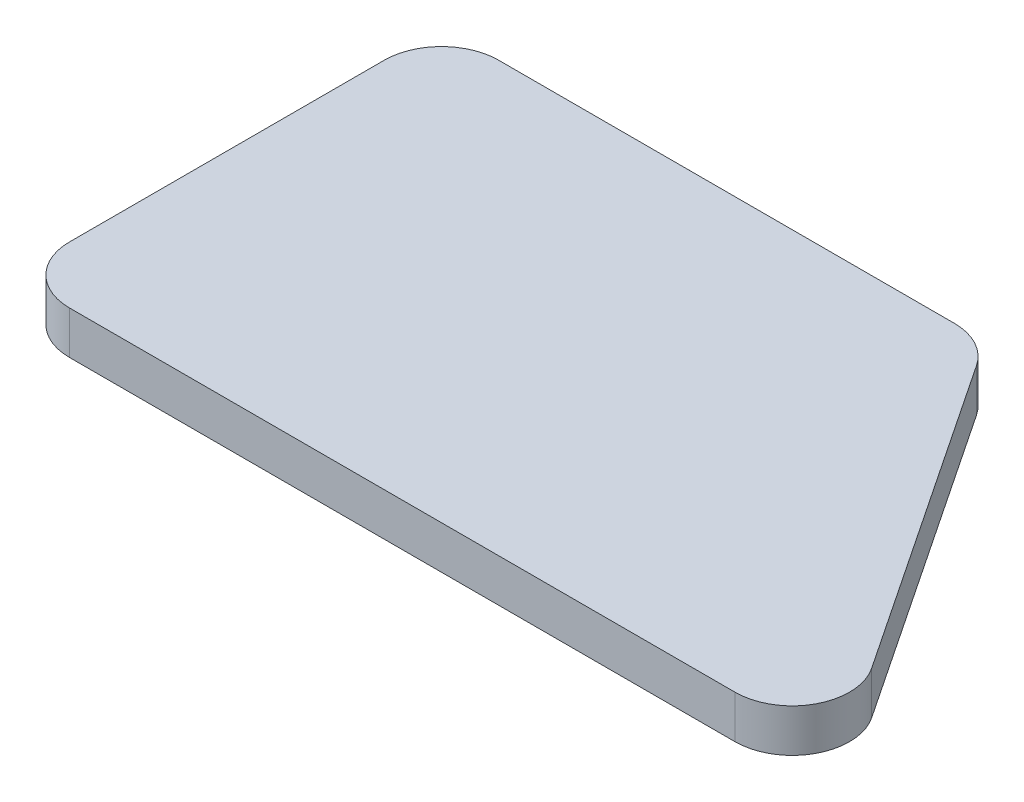
SolidWorks part; units mm, degrees
ref_plane "前视基准面" through (0, 0, 0) normal (0, 0, 1) x (1, 0, 0)
ref_plane "上视基准面" through (0, 0, 0) normal (0, 1, 0) x (1, 0, 0)
ref_plane "右视基准面" through (0, 0, 0) normal (1, 0, 0) x (0, 0, -1)
other "Configuration Table"
sketch "草图1" plane through (0, 0, 0) normal (0, 1, 0) x (1, 0, 0)
  line L0 (-1.0704, 0) -> (-17, 0)
  line L1 (-19, -2) -> (-19, -13)
  line L2 (-17, -15) -> (6.263, -15)
  line L3 (0.5937, -0.8906) -> (7.9271, -11.8906)
  arc A0 (6.263, -15) -> (7.9271, -11.8906) centre (6.263, -13) ccw
  arc A1 (-1.0704, 0) -> (0.5937, -0.8906) centre (-1.0704, -2) cw
  arc A2 (-19, -13) -> (-17, -15) centre (-17, -13) ccw
  arc A3 (-17, 0) -> (-19, -2) centre (-17, -2) ccw
  point P7 (10, -15)
  point P10 (0, 0)
  point P13 (-19, -15)
  point P16 (-19, 0)
  dimension "D4" = 2
  dimension "D1" = 19
  dimension "D2" = 15
  dimension "D3" = 29
extrude "凸台-拉伸1" add sketch "草图1" along normal blind 1.5
